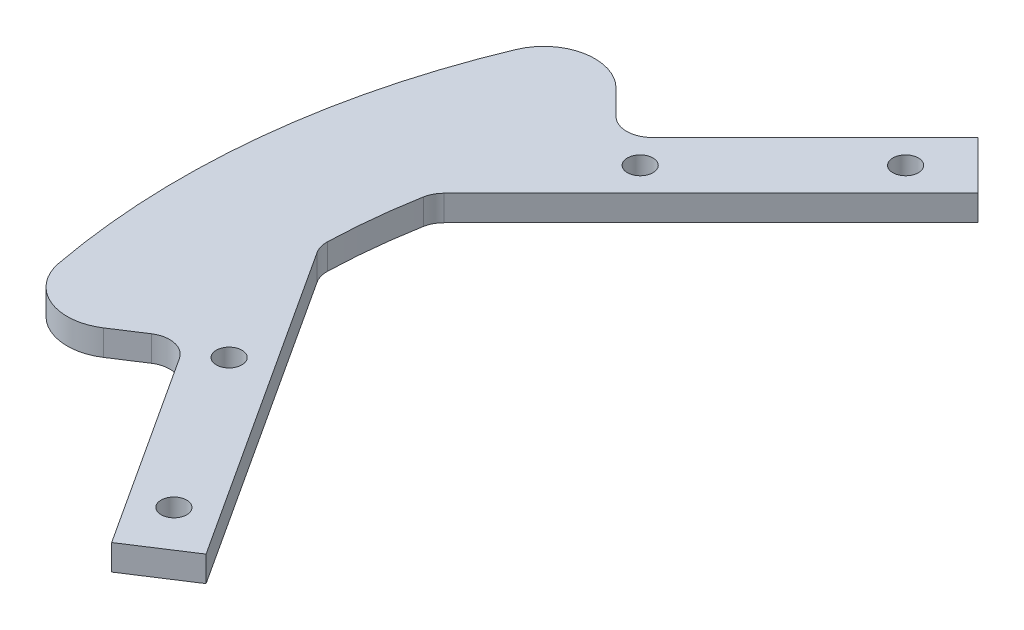
SolidWorks part; units mm, degrees
ref_plane "Front Plane" through (0, 0, 0) normal (0, 0, 1) x (1, 0, 0)
ref_plane "Top Plane" through (0, 0, 0) normal (0, 1, 0) x (1, 0, 0)
ref_plane "Right Plane" through (0, 0, 0) normal (1, 0, 0) x (0, 0, -1)
sketch "Sketch1" plane through (0, 0, 0) normal (0, 1, 0) x (1, 0, 0)
  line L0 (-74.629, 40.6879) -> (-63.6396, 29.6985)
  line L1 (-63.6396, 29.6985) -> (-42.4264, 50.9117)
  line L2 (-42.4264, 50.9117) -> (-36.7696, 45.2548)
  line L3 (-36.7696, 45.2548) -> (-68.725, 13.2994)
  line L5 (-69.9883, 1.28) -> (-45.3751, -36.6211)
  line L6 (-45.3751, -36.6211) -> (-52.0844, -40.9782)
  line L7 (-52.0844, -40.9782) -> (-68.4236, -15.8181)
  line L8 (-68.4236, -15.8181) -> (-81.4577, -24.2825)
  line L9 (0, 0) -> (-85, 0) construction
  line L10 (-43.8406, 43.8406) -> (0, 0) construction
  line L11 (-51.9976, -33.7676) -> (0, 0) construction
  arc A0 (-74.629, 40.6879) -> (-81.4577, -24.2825) centre (0, 0) ccw
  circle A1 centre (-43.8406, 43.8406) radius 1.5
  circle A2 centre (-59.397, 28.2843) radius 1.5
  circle A3 centre (-51.9976, -33.7676) radius 1.5
  circle A4 centre (-63.9796, -15.3169) radius 1.5
  arc A5 (-68.725, 13.2994) -> (-69.9883, 1.28) centre (0, 0) ccw
  dimension "D1" = 85
  dimension "D7" = 3
  dimension "D17" = 70
  dimension "D2" = 8
  dimension "D3" = 4
  dimension "D4" = 4
  dimension "D5" = 24
  dimension "D6" = 24
  dimension "D8" = 6
  dimension "D9" = 22
  dimension "D10" = 22
  dimension "D11" = 6
  dimension "D12" = 4
  dimension "D13" = 4
  dimension "D14" = 45
  dimension "D15" = 33
  dimension "D16" = 66
extrude "Boss-Extrude1" add sketch "Sketch1" along normal blind 3
fillet "Fillet1" radius 6 2 edges at (-74.629, 1.5, -40.6879) (-81.4577, 1.5, 24.2825)
fillet "Fillet2" radius 3 4 edges at (-69.9883, 1.5, -1.28) (-68.725, 1.5, -13.2994) (-63.6396, 1.5, -29.6985) (-68.4236, 1.5, 15.8181)
